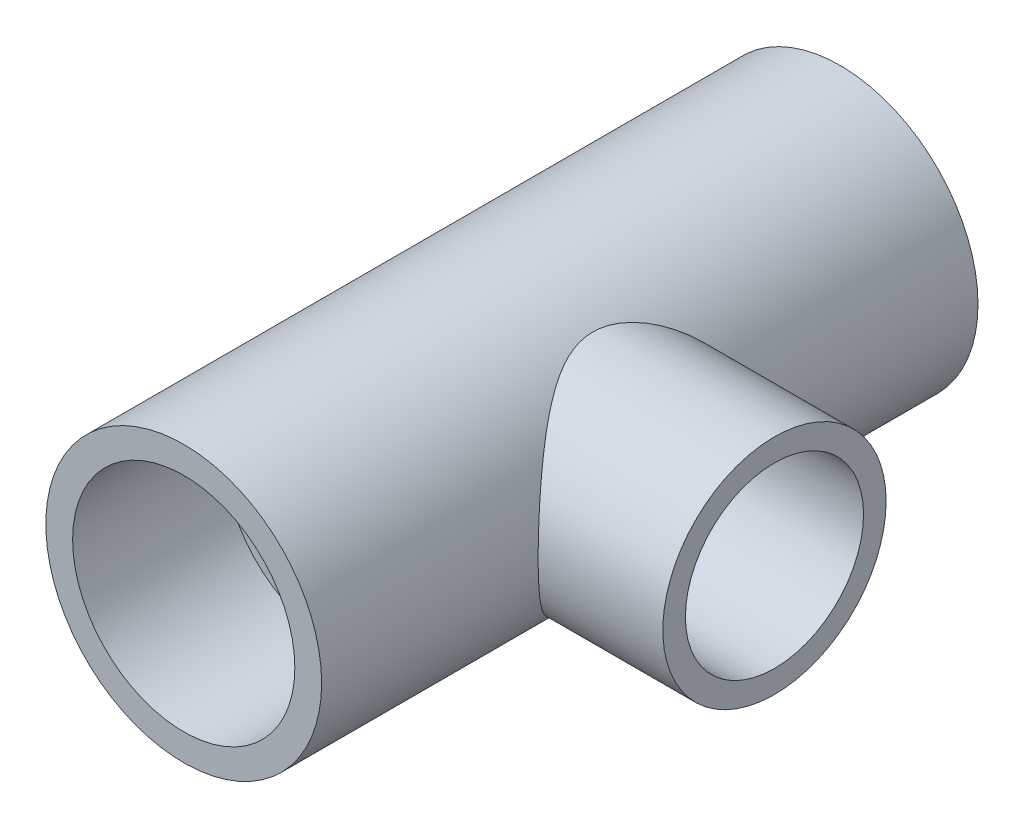
SolidWorks part; units mm, degrees
ref_plane "Front Plane" through (0, 0, 0) normal (0, 0, 1) x (1, 0, 0)
ref_plane "Top Plane" through (0, 0, 0) normal (0, 1, 0) x (1, 0, 0)
ref_plane "Right Plane" through (0, 0, 0) normal (1, 0, 0) x (0, 0, -1)
sketch "Sketch1" plane through (0, 0, 0) normal (0, 0, 1) x (1, 0, 0)
  circle A0 centre (0, 0) radius 656.5
  circle A1 centre (0, 0) radius 412
  dimension "D1" = 1313
  dimension "D2" = 824
extrude "Boss-Extrude1" add sketch "Sketch1" along normal blind 3125
sketch "Sketch2" plane through (0, 0, 3125) normal (0, 0, 1) x (1, 0, 0)
  circle A0 centre (0, 0) radius 529
  dimension "D1" = 1058
extrude "Cut-Extrude1" cut sketch "Sketch2" against normal blind 720
sketch "Sketch3" plane through (0, 0, 0) normal (0, 0, -1) x (-1, 0, 0)
  circle A0 centre (0, 0) radius 529
  dimension "D1" = 1058
extrude "Cut-Extrude2" cut sketch "Sketch3" against normal blind 720
sketch "Sketch7" plane through (0, 0, 0) normal (1, 0, 0) x (0, 0, -1)
  line L0 (-1562.5, 656.5) -> (-1562.5, -656.5) construction
  line L1 (0, 656.5) -> (-3125, 656.5) construction
  line L2 (-3125, -656.5) -> (0, -656.5) construction
  circle A0 centre (-1562.5, 0) radius 531.5
  circle A1 centre (-1562.5, 0) radius 311
  dimension "D1" = 1063
  dimension "D2" = 622
extrude "Boss-Extrude3" add sketch "Sketch7" along normal blind 1250
sketch "Sketch8" plane through (0, 0, 0) normal (1, 0, 0) x (0, 0, -1)
  circle A0 centre (-1562.5, 0) radius 311
  dimension "D1" = 622
extrude "Cut-Extrude7" cut sketch "Sketch8" along normal blind 1250
sketch "Sketch10" plane through (1250, 0, 0) normal (1, 0, 0) x (0, 0, -1)
  circle A0 centre (-1562.5, 0) radius 424
  dimension "D1" = 848
extrude "Cut-Extrude8" cut sketch "Sketch10" against normal blind 690
